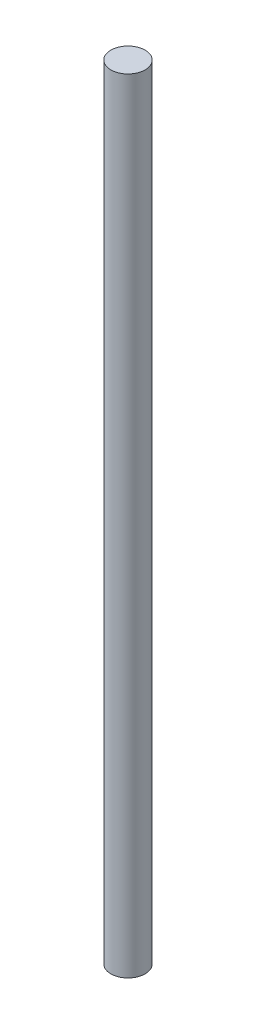
SolidWorks part; units mm, degrees
ref_plane "Front Plane" through (0, 0, 0) normal (0, 0, 1) x (1, 0, 0)
ref_plane "Top Plane" through (0, 0, 0) normal (0, 1, 0) x (1, 0, 0)
ref_plane "Right Plane" through (0, 0, 0) normal (1, 0, 0) x (0, 0, -1)
sketch "Sketch1" plane through (0, 0, 0) normal (0, 1, 0) x (1, 0, 0)
  circle A0 centre (0, 0) radius 10
  dimension "D1" = 20
extrude "Boss-Extrude1" add sketch "Sketch1" along normal blind 457
